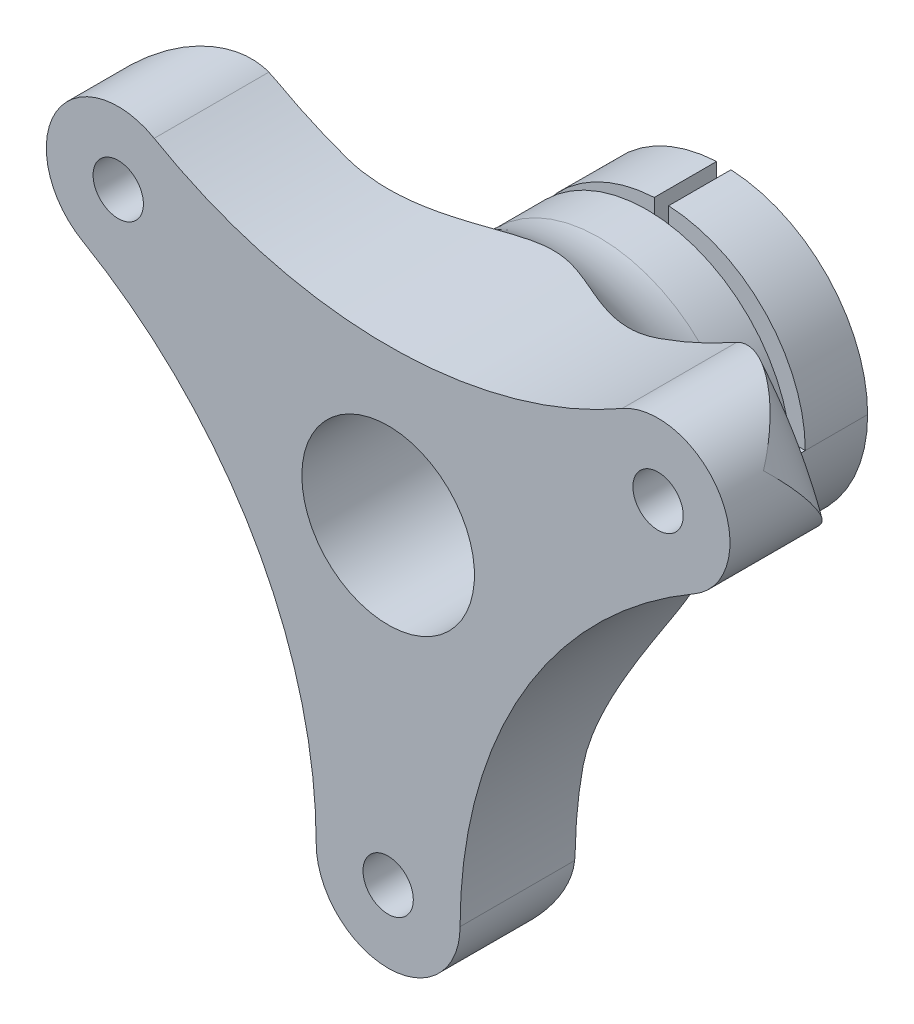
SolidWorks part; units mm, degrees
ref_plane "Front Plane" through (0, 0, 0) normal (0, 0, 1) x (1, 0, 0)
ref_plane "Top Plane" through (0, 0, 0) normal (0, 1, 0) x (1, 0, 0)
ref_plane "Right Plane" through (0, 0, 0) normal (1, 0, 0) x (0, 0, -1)
sketch "Sketch1" plane through (0, 0, 0) normal (0, 1, 0) x (1, 0, 0)
  line L0 (0, 0) -> (40, 0)
  line L1 (0, 0) -> (0, 35)
  line L2 (0, 35) -> (15, 35)
  line L7 (15, 35) -> (15, 22)
  line L9 (40, 4.5) -> (40, 0)
  line L10 (25, 12) -> (32.5, 12)
  arc A4 (25, 12) -> (15, 22) centre (25, 22) cw
  arc A5 (32.5, 12) -> (40, 4.5) centre (32.5, 4.5) cw
  point P11 (40, 12)
  point P12 (40, 12)
  dimension "D6" = 7.5
  dimension "D5" = 10
  dimension "D1" = 40
  dimension "D2" = 35
  dimension "D3" = 15
  dimension "D4" = 12
revolve "Revolve1" add sketch "Sketch1" angle 360 about L1
sketch "Sketch2" plane through (0, 0, -35) normal (0, 0, -1) x (-1, 0, 0)
  circle A0 centre (0, 0) radius 11.1125
  dimension "D1" = 22.225
extrude "Cut-Extrude1" cut sketch "Sketch2" against normal blind 15.875 contours A0
sketch "Sketch3" plane through (0, 0, 0) normal (0, 1, 0) x (1, 0, 0)
  line L1 (-17.5, 28.5) -> (17.5, 28.5)
  line L2 (-17.5, 28.5) -> (-17.5, 27)
  line L3 (-17.5, 27) -> (17.5, 27)
  line L4 (17.5, 28.5) -> (17.5, 27)
  dimension "D1" = 1.5
  dimension "D2" = 35
  dimension "D3" = 17.5
  dimension "D4" = 27
extrude "Cut-Extrude2" cut sketch "Sketch3" along normal blind 15.875
sketch "Sketch4" plane through (0, 0, -35) normal (0, 0, -1) x (-1, 0, 0)
  line L1 (-0.75, 17.5) -> (0.75, 17.5)
  line L2 (-0.75, 17.5) -> (-0.75, -17.5)
  line L3 (-0.75, -17.5) -> (0.75, -17.5)
  line L4 (0.75, 17.5) -> (0.75, -17.5)
  dimension "D1" = 1.5
  dimension "D2" = 0.75
  dimension "D3" = 35
  dimension "D4" = 17.5
extrude "Cut-Extrude3" cut sketch "Sketch4" against normal up to surface (8 mm away) up to face at (0, 6.5281, -27)
sketch "Sketch5" plane through (0, 0, 0) normal (0, 0, 1) x (1, 0, 0)
  circle A0 centre (0, 0) radius 32.5
  circle A1 centre (-28.1458, 16.25) radius 2.625
  circle A2 centre (28.1458, 16.25) radius 2.625
  circle A3 centre (0, -32.5) radius 2.625
  point P3 (0, -32.5)
  point P7 (-28.1458, 16.25)
  point P8 (28.1458, 16.25)
  point P9 (0, 0)
  dimension "D1" = 65
  dimension "D3" = 5.25
  dimension "D4" = 5.25
  dimension "D5" = 5.25
  dimension "D2" = 3
sketch "Sketch8" plane through (0, 0, 0) normal (0, 0, 1) x (1, 0, 0)
  arc A0 (-24.3958, 22.7452) -> (-31.8958, 9.7548) centre (-28.1458, 16.25) ccw
  arc A1 (31.8958, 9.7548) -> (24.3958, 22.7452) centre (28.1458, 16.25) ccw
  arc A2 (-7.5, -32.5) -> (7.5, -32.5) centre (0, -32.5) ccw
  arc A3 (-24.3958, 22.7452) -> (24.3958, 22.7452) centre (0, 65) ccw
  arc A4 (-31.8958, 9.7548) -> (-7.5, -32.5) centre (-56.2917, -32.5) cw
  arc A5 (31.8958, 9.7548) -> (7.5, -32.5) centre (56.2917, -32.5) ccw
  dimension "D1" = 15
  dimension "D2" = 15
  dimension "D3" = 15
  dimension "D4" = 15
  dimension "D5" = 15
extrude "Cut-Extrude4" cut sketch "Sketch8" against normal through all flip side to cut
sketch "Sketch9" plane through (0, 0, -19.125) normal (0, 0, -1) x (-1, 0, 0)
  circle A0 centre (0, 0) radius 9
  dimension "D1" = 18
extrude "Cut-Extrude5" cut sketch "Sketch9" against normal through all
extrude "Cut-Extrude7" cut sketch "Sketch5" against normal through all contours A1 | A2 | A3
sketch "Sketch11" plane through (0, 0, -12) normal (0, 0, -1) x (-1, 0, 0)
  circle A0 centre (-28.1458, 16.25) radius 4
  circle A1 centre (28.1458, 16.25) radius 4
  circle A2 centre (0, -32.5) radius 4
  dimension "D1" = 8
  dimension "D2" = 8
  dimension "D3" = 8
extrude "Cut-Extrude8" cut sketch "Sketch11" against normal blind 5 contours A0 | A1 | A2
